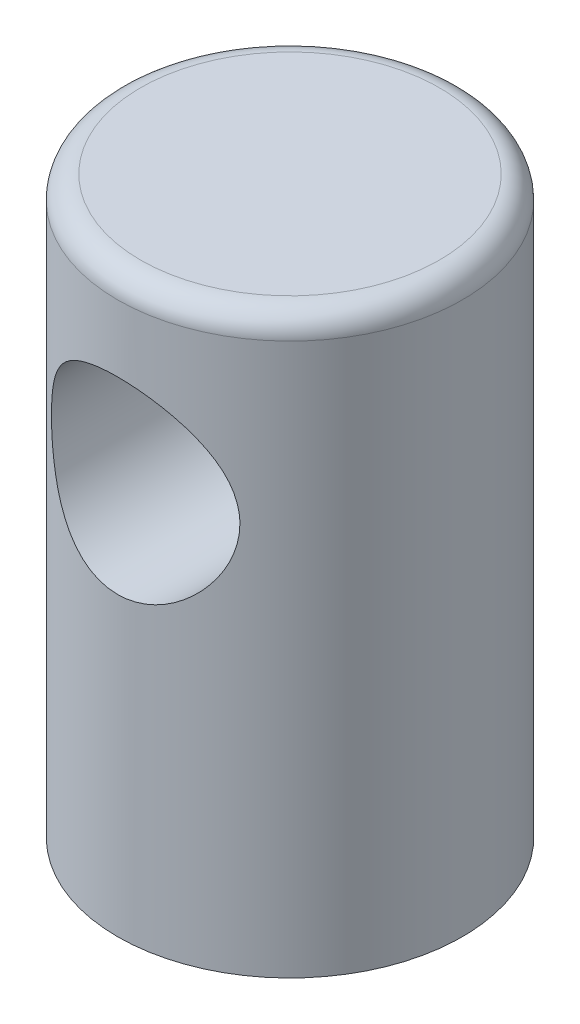
SolidWorks part; units mm, degrees
material "1.4301 (X5CrNi18-10)"
ref_plane "Front Plane" through (0, 0, 0) normal (0, 0, 1) x (1, 0, 0)
ref_plane "Top Plane" through (0, 0, 0) normal (0, 1, 0) x (1, 0, 0)
ref_plane "Right Plane" through (0, 0, 0) normal (1, 0, 0) x (0, 0, -1)
sketch "Sketch1" plane through (0, 0, 0) normal (0, 1, 0) x (1, 0, 0)
  circle A0 centre (0, 0) radius 7.5
  dimension "D1" = 15
extrude "Boss-Extrude1" add sketch "Sketch1" along normal blind 25
fillet "Fillet1" radius 1 1 edges at (0, 25, 7.5)
sketch "Sketch2" plane through (0, 0, 0) normal (0, 0, 1) x (1, 0, 0)
  line L0 (8.25, 0) -> (-8.25, 0) construction
  circle A0 centre (0, 17) radius 4.1
  dimension "D1" = 8.2
  dimension "D2" = 17
extrude "Cut-Extrude1" cut sketch "Sketch2" against normal through all both and the other way through all
hole_wizard "M5 Tapped Hole1" positions "Sketch3" profile "Sketch5" tap size "M5" standard "DIN"
sketch "Sketch3" plane through (0, 0, 0) normal (0, -1, 0) x (-1, 0, 0)
  point P0 (0, 0)
sketch "Sketch5" plane through (0, 0, 0) normal (1, 0, 0) x (0, 0, -1)
  line L0 (0, 0) -> (0, 12.2618)
  line L1 (0, 12.2618) -> (2.1, 11)
  line L2 (2.1, 11) -> (2.1, 0)
  line L5 (2.1, 0) -> (0, 0)
  line L10 (0, 12.2618) -> (-2.1, 11) construction
  line L11 (0, -6.35) -> (0, 107.95) construction
  dimension "Tap Drill Dia." = 4.2
  dimension "Tap Drill Depth" = 11
  dimension "Drill Angle" = 118
cosmetic thread "Hole Thread1" parameters "D1"=8, "D2"=5
